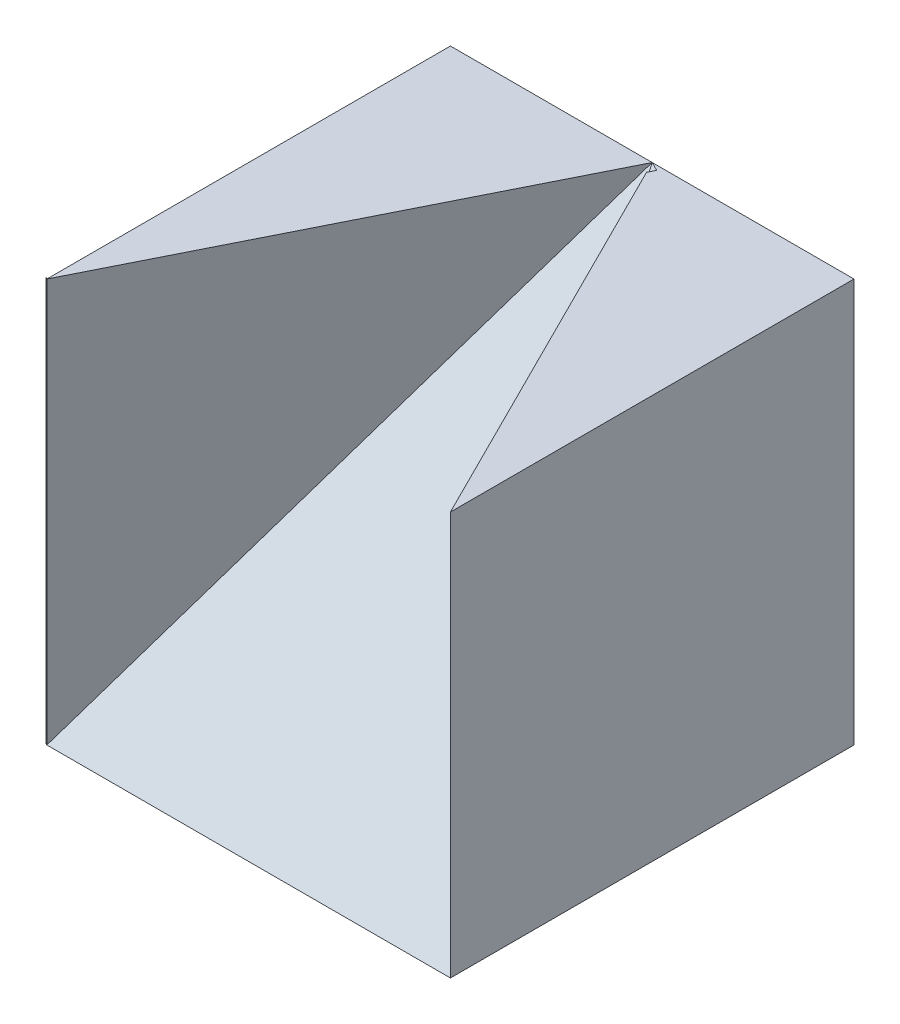
SolidWorks part; units mm, degrees
ref_plane "Front Plane" through (0, 0, 0) normal (0, 0, 1) x (1, 0, 0)
ref_plane "Top Plane" through (0, 0, 0) normal (0, 1, 0) x (1, 0, 0)
ref_plane "Right Plane" through (0, 0, 0) normal (1, 0, 0) x (0, 0, -1)
sketch "Sketch1" plane through (0, 0, 0) normal (0, 0, 1) x (1, 0, 0)
  line L1 (0, 0) -> (40, 0)
  line L2 (0, 0) -> (0, 40)
  line L3 (0, 40) -> (40, 40)
  line L4 (40, 0) -> (40, 40)
  dimension "D1" = 40
  dimension "D2" = 40
extrude "Boss-Extrude1" add sketch "Sketch1" along normal blind 40
ref_plane "Plane1" through (0, 20, 20) normal (0, 0.7071, 0.7071) x (1, 0, 0)
sketch "Sketch2" plane through (0, 20, 20) normal (0, 0.7071, 0.7071) x (1, 0, 0)
  line L0 (0, -28.2843) -> (20, 28.2843)
  line L1 (40, 28.2843) -> (0, 28.2843) construction
  line L2 (20, 28.2843) -> (40, -28.2843)
  line L3 (40, -28.2843) -> (0, -28.2843)
  line L4 (0, -28.2843) -> (-0.3185, -27.7511)
extrude "Cut-Extrude1" cut sketch "Sketch2" along normal blind 40 contours L3 L2 L0
ref_plane "Plane2" through (16, 0, 8) normal (-0.8944, 0, -0.4472) x (-0.4472, 0, 0.8944)
ref_plane "Plane3" through (16, 0, -8) normal (-0.8944, 0, 0.4472) x (0.4472, 0, 0.8944)
sketch "Sketch4" plane through (16, 0, -8) normal (-0.8944, 0, 0.4472) x (0.4472, 0, 0.8944)
  line L0 (8.9443, 40) -> (53.6656, 40)
  line L1 (53.6656, 40) -> (53.6656, 0)
  line L2 (8.9443, 40) -> (53.6656, 0)
extrude "Cut-Extrude3" cut sketch "Sketch4" along normal blind 40
sketch "Sketch5" plane through (16, 0, 8) normal (-0.8944, 0, -0.4472) x (-0.4472, 0, 0.8944)
  line L0 (35.7771, 0) -> (-8.9443, 40)
  line L1 (-8.9443, 40) -> (29.3481, 45.4201)
  line L2 (29.3481, 45.4201) -> (35.7771, 0)
  dimension "D1" = 45.8728
extrude "Cut-Extrude5" cut sketch "Sketch5" against normal blind 1
sketch "Sketch6" plane through (16, 0, 8) normal (-0.8944, 0, -0.4472) x (-0.4472, 0, 0.8944)
  line L0 (35.7771, 0) -> (-8.9443, 40)
  line L1 (-8.9443, 40) -> (33.3262, 17.3153) construction
  line L2 (35.7771, 0) -> (-8.9443, 40) construction
  line L3 (-8.9443, 40) -> (35.7771, 40)
  line L4 (35.7771, 40) -> (35.7771, 0)
  line L5 (35.7771, 0) -> (36.2421, -0.5924)
extrude "Boss-Extrude2" add sketch "Sketch6" along normal blind 26 contours L4 L3 L0
sketch "Sketch7" plane through (16, 0, 8) normal (0.8944, 0, 0.4472) x (0.4472, 0, -0.8944)
  line L0 (-35.7771, 40) -> (-35.7771, 0)
  line L1 (-35.7771, 0) -> (-35.7771, 40)
  line L2 (8.9443, 40) -> (-35.7771, 0)
  line L3 (-35.7771, 0) -> (8.9443, 40) construction
  line L4 (8.9443, 40) -> (-35.7771, 40) construction
  line L5 (-35.7771, 31.2064) -> (2.9789, 34.6644)
  point P13 (-34.4248, 38.8974)
  line M1 (-35.7771, 0) -> (8.9443, 40)
  line M4 (-35.7771, 16) -> (-33.3262, 17.3153)
  line M5 (-33.3262, 17.3153) -> (-35.7771, 0)
  dimension "D1" = 38.756
  dimension "D2" = 8.7936
extrude "Cut-Extrude7" cut sketch "Sketch7" along normal blind 5 contours L5 L1 M4 M5 M1
sketch "Sketch8" plane through (-15.6857, 4.9646, 31.3715) normal (0.4428, -0.1401, -0.8856) x (-0.8966, -0.0692, -0.4374)
  line L0 (-21.7498, 8.4583) -> (-18.7167, 11.1928)
  line L1 (-18.7167, 11.1928) -> (-17.4943, -6.2523)
  line L2 (-17.4943, -6.2523) -> (-21.7498, 8.4583)
extrude "Cut-Extrude8" cut sketch "Sketch8" against normal blind 5
sketch "Sketch9" plane through (15.9709, -3.8567, 8.5958) normal (-0.8613, 0.208, -0.4636) x (-0.4506, 0.1088, 0.8861)
  line L0 (35.4425, 15.01) -> (34.948, 15.3057)
  line L1 (34.948, 15.3057) -> (35.4425, 0)
  line L2 (35.4425, 15.01) -> (35.4425, 0) construction
  line L3 (35.4425, 0) -> (34.948, 15.3057) construction
  line L4 (35.4425, 0) -> (35.4425, 15.01)
extrude "Cut-Extrude9" cut sketch "Sketch9" against normal blind 5
sketch "Sketch10" plane through (0, 0, 0) normal (0, 0, -1) x (-1, 0, 0)
  line L1 (-40, 0) -> (0, 0)
  line L2 (-40, 0) -> (-40, 40)
  line L3 (-40, 40) -> (0, 40)
  line L4 (0, 0) -> (0, 40)
  dimension "D1" = 40
  dimension "D2" = 40
extrude "Cut-Extrude10" cut sketch "Sketch10" along normal blind 50
sketch "Sketch11" plane through (0, 0, 0) normal (-1, 0, 0) x (0, 0, 1)
  line L1 (-16.8231, 0) -> (39.9164, 0)
  line L2 (-16.8231, 0) -> (-16.8231, 49.0263)
  line L3 (-16.8231, 49.0263) -> (39.9164, 49.0263)
  line L4 (39.9164, 0) -> (39.9164, 49.0263)
  dimension "D1" = 56.7395
  dimension "D2" = 49.0263
  dimension "D3" = 16.8231
  dimension "D4" = 10.4148
extrude "Cut-Extrude11" cut sketch "Sketch11" along normal blind 50
